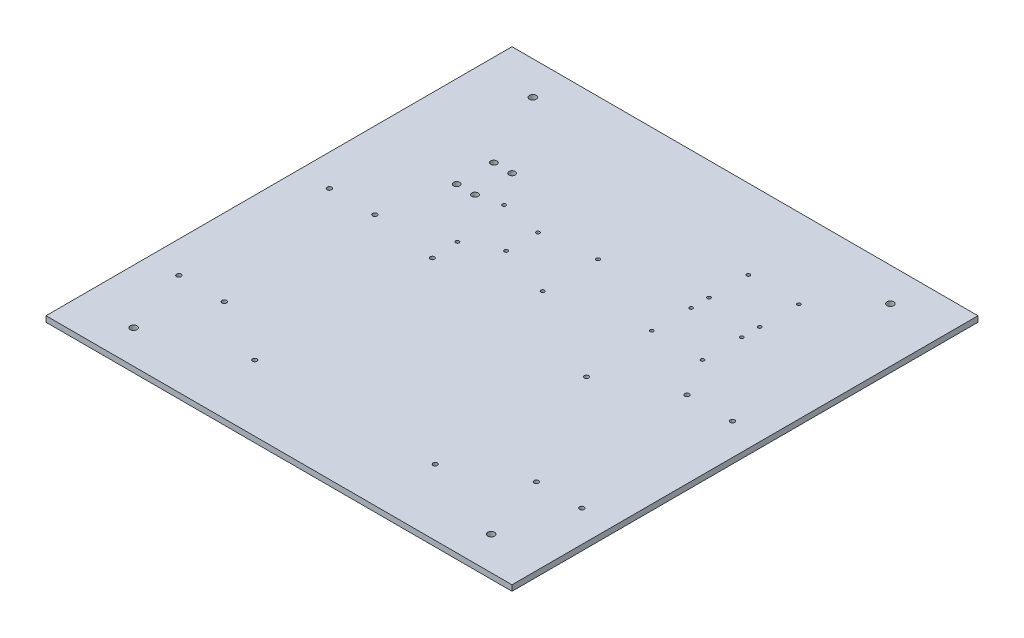
SolidWorks part; units mm, degrees
ref_plane "前基準面" through (0, 0, 0) normal (0, 0, 1) x (1, 0, 0)
ref_plane "上基準面" through (0, 0, 0) normal (0, 1, 0) x (1, 0, 0)
ref_plane "右基準面" through (0, 0, 0) normal (1, 0, 0) x (0, 0, -1)
sketch "草圖1" plane through (0, 0, 0) normal (0, 1, 0) x (1, 0, 0)
  line L1 (-205, 205) -> (205, 205)
  line L2 (-205, 205) -> (-205, -205)
  line L3 (-205, -205) -> (205, -205)
  line L4 (205, 205) -> (205, -205)
  line L5 (0, -205) -> (0, 205) construction
  line L6 (-205, 0) -> (205, 0) construction
  point P0 (0, 0)
  dimension "D1" = 410
  dimension "D2" = 410
extrude "填料-伸長1" add sketch "草圖1" along normal blind 5
sketch "草圖2" plane through (0, 5, 0) normal (0, 1, 0) x (1, 0, 0)
  line L0 (0, 0) -> (0, 285.104) construction
  line L1 (0, 0) -> (407.1184, 0) construction
  circle A0 centre (-157.3, 175.6) radius 3
  circle A1 centre (157.3, 175.6) radius 3
  circle A2 centre (-157.3, -175.6) radius 3
  circle A3 centre (157.3, -175.6) radius 3
  dimension "D1" = 314.6
  dimension "D3" = 351.2
  dimension "D2" = 157.3
  dimension "D4" = 351.2
  dimension "D5" = 175.6
  dimension "D6" = 175.6
extrude "鋁擠螺絲孔(4邊" cut sketch "草圖2" against normal blind 5
sketch "TX2位置" plane through (0, 5, 0) normal (0, 1, 0) x (1, 0, 0)
  line L5 (-85.1, 18.868) -> (85.1, 18.868)
  line L6 (-85.1, 18.868) -> (-85.1, -151.332)
  line L7 (-85.1, -151.332) -> (85.1, -151.332)
  line L8 (85.1, 18.868) -> (85.1, -151.332)
  dimension "D1" = 170.2
  dimension "D2" = 170.2
  dimension "D3" = 85.1
sketch "草圖11" plane through (0, 5, 0) normal (0, 1, 0) x (1, 0, 0)
  line L0 (-157.3, 175.6) -> (-157.3, -175.6) construction
  line L1 (-157.3, -175.6) -> (157.3, -175.6) construction
  line L2 (157.3, -175.6) -> (157.3, 175.6) construction
  line L3 (157.3, 175.6) -> (-157.3, 175.6) construction
sketch "電池座位置" plane through (0, 5, 0) normal (0, 1, 0) x (1, 0, 0)
  line L0 (157.3, -175.6) -> (157.3, 175.6) construction
  line L1 (123.25, 11.6637) -> (191.35, 11.6637)
  line L2 (123.25, 11.6637) -> (123.25, -110.8363)
  line L3 (123.25, -110.8363) -> (191.35, -110.8363)
  line L4 (191.35, 11.6637) -> (191.35, -110.8363)
  line L5 (-191.35, 11.6637) -> (-123.25, 11.6637)
  line L6 (-191.35, 11.6637) -> (-191.35, -110.8363)
  line L7 (-191.35, -110.8363) -> (-123.25, -110.8363)
  line L8 (-123.25, 11.6637) -> (-123.25, -110.8363)
  line L9 (-191.35, 11.6637) -> (-123.25, 11.6637)
  line L10 (-191.35, 11.6637) -> (-191.35, 21.6637)
  line L11 (-191.35, 21.6637) -> (-123.25, 21.6637)
  line L12 (-123.25, 11.6637) -> (-123.25, 21.6637)
  line L13 (-191.35, -110.8363) -> (-123.25, -110.8363)
  line L14 (-191.35, -110.8363) -> (-191.35, -120.8363)
  line L15 (-191.35, -120.8363) -> (-123.25, -120.8363)
  line L16 (-123.25, -110.8363) -> (-123.25, -120.8363)
  line L17 (123.25, 11.6637) -> (191.35, 11.6637)
  line L18 (123.25, 11.6637) -> (123.25, 21.6637)
  line L19 (123.25, 21.6637) -> (191.35, 21.6637)
  line L20 (191.35, 11.6637) -> (191.35, 21.6637)
  line L21 (123.25, -110.8363) -> (191.35, -110.8363)
  line L22 (123.25, -110.8363) -> (123.25, -120.8363)
  line L23 (123.25, -120.8363) -> (191.35, -120.8363)
  line L24 (191.35, -110.8363) -> (191.35, -120.8363)
  line L25 (-157.3, 175.6) -> (-157.3, -175.6) construction
  dimension "D1" = 68.1
  dimension "D2" = 68.1
  dimension "D3" = 122.5
  dimension "D4" = 122.5
  dimension "D5" = 10
  dimension "D6" = 10
  dimension "D7" = 10
  dimension "D8" = 10
  dimension "D9" = 34.05
  dimension "D10" = 34.05
  dimension "D11" = 0
sketch "草圖5" plane through (0, 5, 0) normal (0, 1, 0) x (1, 0, 0)
  line L0 (-85.1, -151.332) -> (85.1, -151.332) construction
  line L1 (-85.1, 18.868) -> (-85.1, -151.332) construction
  line L3 (85.1, 18.868) -> (85.1, -151.332) construction
  line L4 (-85.1, 18.868) -> (85.1, 18.868) construction
  circle A0 centre (-79, 8.968) radius 1.9
  circle A1 centre (79.4, -13.832) radius 1.9
  circle A2 centre (-79.4, -146.932) radius 1.9
  circle A3 centre (79.4, -146.932) radius 1.9
  circle A4 centre (-79.4, -146.932) radius 1.9
  dimension "D1" = 4.4
  dimension "D2" = 5.7
  dimension "D3" = 5.7
  dimension "D4" = 4.4
  dimension "D5" = 9.9
  dimension "D6" = 6.1
  dimension "D7" = 32.7
  dimension "D8" = 5.7
extrude "TX2螺絲孔" cut sketch "草圖5" against normal blind 5 contours A0 | A2 | A3 | A1
sketch "緊急開關位置" plane through (0, 5, 0) normal (0, 1, 0) x (1, 0, 0)
  line L1 (-131.0518, 108.6267) -> (-102.0518, 108.6267)
  line L2 (-131.0518, 108.6267) -> (-131.0518, 75.9267)
  line L3 (-131.0518, 75.9267) -> (-102.0518, 75.9267)
  line L4 (-102.0518, 108.6267) -> (-102.0518, 75.9267)
  dimension "D1" = 32.7
  dimension "D2" = 29
sketch "Arduino Mega位置" plane through (0, 5, 0) normal (0, 1, 0) x (1, 0, 0)
  line L1 (-94.615, 83.4119) -> (7.385, 83.4119)
  line L2 (-94.615, 83.4119) -> (-94.615, 29.7119)
  line L3 (-94.615, 29.7119) -> (7.385, 29.7119)
  line L4 (7.385, 83.4119) -> (7.385, 29.7119)
  dimension "D1" = 102
  dimension "D2" = 53.7
sketch "麵包板位置" plane through (0, 5, 0) normal (0, 1, 0) x (1, 0, 0)
  line L1 (-89.7544, 139.6977) -> (-7.3544, 139.6977)
  line L2 (-89.7544, 139.6977) -> (-89.7544, 94.5977)
  line L3 (-89.7544, 94.5977) -> (-7.3544, 94.5977)
  line L4 (-7.3544, 139.6977) -> (-7.3544, 94.5977)
  dimension "D1" = 82.4
  dimension "D2" = 45.1
sketch "洞洞" plane through (0, 5, 0) normal (0, 1, 0) x (1, 0, 0)
  line L1 (20.9468, 116.217) -> (60.9468, 116.217)
  line L2 (20.9468, 116.217) -> (20.9468, 66.217)
  line L3 (20.9468, 66.217) -> (60.9468, 66.217)
  line L4 (60.9468, 116.217) -> (60.9468, 66.217)
  dimension "D1" = 40
  dimension "D2" = 50
sketch "草圖6" plane through (0, 5, 0) normal (0, 1, 0) x (1, 0, 0)
  line L0 (-94.615, 83.4119) -> (7.385, 83.4119) construction
  line L1 (-94.615, 29.7119) -> (7.385, 29.7119) construction
  circle A0 centre (-80.3539, 32.2519) radius 1.562
  circle A1 centre (-87.8469, 80.8719) radius 1.562
  circle A2 centre (-51.9949, 74.8279) radius 1.562
  circle A3 centre (-51.9949, 46.8119) radius 1.562
  circle A4 centre (-5.2209, 80.8719) radius 1.562
  circle A5 centre (-5.2209, 32.2519) radius 1.562
  point P16 (-5.2209, 32.2519)
  point P17 (0, 0)
  point P18 (-5.2209, 32.2519)
  point P19 (-51.9949, 38.0727)
  dimension "D1" = 2.54
  dimension "D5" = 3.124
  dimension "D6" = 3.124
  dimension "D7" = 3.124
  dimension "D8" = 3.124
  dimension "D9" = 3.124
  dimension "D10" = 3.124
  dimension "D2" = 2.54
  dimension "D3" = 2.54
  dimension "D4" = 2.54
  dimension "D11" = 35.852
  dimension "D12" = 82.626
  dimension "D13" = 75.133
  dimension "D14" = 28.016
  dimension "D15" = 17.1
extrude "ArduinoMega螺絲孔" cut sketch "草圖6" against normal blind 10
sketch "H bridge*2" plane through (0, 5, 0) normal (0, 1, 0) x (1, 0, 0)
  line L1 (71.2842, 139.3054) -> (119.0842, 139.3054)
  line L2 (71.2842, 139.3054) -> (71.2842, 96.1054)
  line L3 (71.2842, 96.1054) -> (119.0842, 96.1054)
  line L4 (119.0842, 139.3054) -> (119.0842, 96.1054)
  line L5 (71.2842, 89.0224) -> (119.0842, 89.0224)
  line L6 (71.2842, 89.0224) -> (71.2842, 45.8224)
  line L7 (71.2842, 45.8224) -> (119.0842, 45.8224)
  line L8 (119.0842, 89.0224) -> (119.0842, 45.8224)
  dimension "D1" = 43.2
  dimension "D2" = 47.8
  dimension "D3" = 47.8
  dimension "D4" = 43.2
  dimension "D5" = 0
sketch "草圖9" plane through (0, 5, 0) normal (0, 1, 0) x (1, 0, 0)
  line L0 (95.1842, 139.3054) -> (95.1842, 45.8224) construction
  line L1 (71.2842, 139.3054) -> (119.0842, 139.3054) construction
  line L2 (71.2842, 45.8224) -> (119.0842, 45.8224) construction
  line L3 (71.2842, 117.7054) -> (119.0842, 117.7054) construction
  line L4 (71.2842, 139.3054) -> (71.2842, 96.1054) construction
  line L5 (119.0842, 139.3054) -> (119.0842, 96.1054) construction
  line L6 (71.2842, 67.4224) -> (119.0842, 67.4224) construction
  line L7 (71.2842, 89.0224) -> (71.2842, 45.8224) construction
  line L8 (119.0842, 89.0224) -> (119.0842, 45.8224) construction
  circle A0 centre (72.8842, 135.0054) radius 1.5
  circle A1 centre (117.4842, 135.0054) radius 1.5
  circle A2 centre (72.8842, 100.4054) radius 1.5
  circle A3 centre (117.4842, 100.4054) radius 1.5
  circle A4 centre (72.8842, 84.7224) radius 1.5
  circle A5 centre (72.8842, 50.1224) radius 1.5
  circle A6 centre (117.4842, 84.7224) radius 1.5
  circle A7 centre (117.4842, 50.1224) radius 1.5
  dimension "D1" = 44.6
  dimension "D9" = 44.6
  dimension "D2" = 44.6
  dimension "D3" = 22.3
  dimension "D4" = 22.3
  dimension "D5" = 34.6
  dimension "D6" = 34.6
  dimension "D7" = 17.3
  dimension "D8" = 17.3
  dimension "D10" = 22.3
  dimension "D11" = 44.6
  dimension "D12" = 22.3
  dimension "D13" = 34.6
  dimension "D14" = 17.3
  dimension "D15" = 34.6
  dimension "D16" = 17.3
extrude "H bridge 螺絲孔" cut sketch "草圖9" against normal blind 10
sketch "草圖10" plane through (0, 5, 0) normal (0, 1, 0) x (1, 0, 0)
  line L0 (-131.0518, 108.6267) -> (-102.0518, 108.6267) construction
  line L1 (-131.0518, 75.9267) -> (-102.0518, 75.9267) construction
  line L2 (-131.0518, 108.6267) -> (-131.0518, 75.9267) construction
  line L3 (-102.0518, 108.6267) -> (-102.0518, 75.9267) construction
  circle A0 centre (-124.6018, 108.6267) radius 2.75
  circle A1 centre (-108.5018, 108.6267) radius 2.75
  circle A2 centre (-124.6018, 75.9267) radius 2.75
  circle A3 centre (-108.5018, 75.9267) radius 2.75
  dimension "D1" = 5.5
  dimension "D2" = 5.5
  dimension "D3" = 5.5
  dimension "D4" = 5.5
  dimension "D5" = 6.45
  dimension "D6" = 6.45
  dimension "D7" = 6.45
  dimension "D8" = 6.45
extrude "緊急開關螺絲孔" cut sketch "草圖10" against normal blind 10
sketch "電池做螺絲孔" plane through (0, 5, 0) normal (0, 1, 0) x (1, 0, 0)
  line L0 (-191.35, 11.6637) -> (-123.25, 11.6637) construction
  line L1 (-191.35, -120.8363) -> (-123.25, -120.8363) construction
  line L3 (-157.3, 175.6) -> (-157.3, -175.6) construction
  line L4 (157.3, -175.6) -> (157.3, 175.6) construction
  circle A0 centre (-137.3, 16.6637) radius 2
  circle A1 centre (-177.3, 16.6637) radius 2
  circle A2 centre (-177.3, -115.8363) radius 2
  circle A3 centre (-137.3, -115.8363) radius 2
  circle A4 centre (137.3, 16.6637) radius 2
  circle A5 centre (177.3, 16.6637) radius 2
  circle A6 centre (137.3, -115.8363) radius 2
  circle A7 centre (177.3, -115.8363) radius 2
  dimension "D5" = 4
  dimension "D6" = 4
  dimension "D7" = 4
  dimension "D8" = 4
  dimension "D13" = 40
  dimension "D1" = 5
  dimension "D2" = 5
  dimension "D3" = 5
  dimension "D4" = 5
  dimension "D9" = 40
  dimension "D10" = 20
  dimension "D11" = 40
  dimension "D12" = 20
  dimension "D14" = 20
  dimension "D15" = 40
  dimension "D16" = 20
extrude "除料-伸長4" cut sketch "電池做螺絲孔" against normal blind 10
